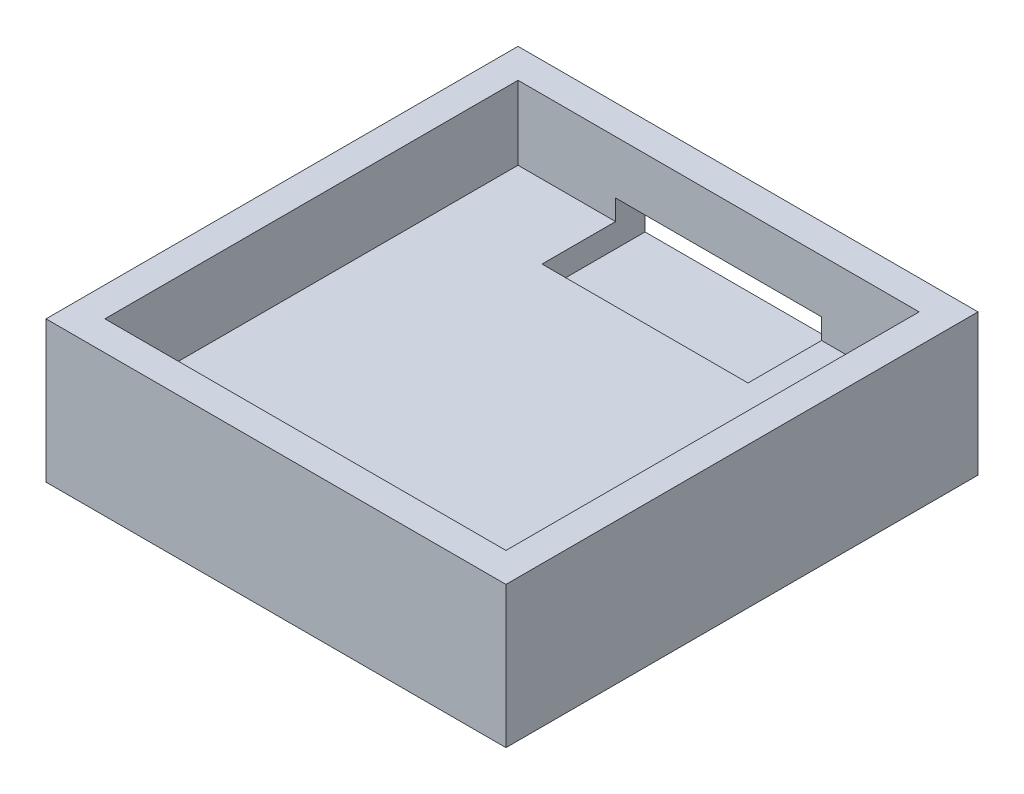
SolidWorks part; units mm, degrees
ref_plane "Front Plane" through (0, 0, 0) normal (0, 0, 1) x (1, 0, 0)
ref_plane "Top Plane" through (0, 0, 0) normal (0, 1, 0) x (1, 0, 0)
ref_plane "Right Plane" through (0, 0, 0) normal (1, 0, 0) x (0, 0, -1)
sketch "Sketch1" plane through (0, 0, 0) normal (0, 1, 0) x (1, 0, 0)
  line L0 (-10.8283, 7.7152) -> (16.4317, 7.7152)
  line L1 (-9.8283, 6.7152) -> (15.4317, 6.7152)
  line L2 (-9.8283, 6.7152) -> (-9.8283, -19.3648)
  line L3 (-9.8283, -19.3648) -> (15.4317, -19.3648)
  line L4 (15.4317, 6.7152) -> (15.4317, -19.3648)
  line L5 (16.4317, 7.7152) -> (16.4317, -20.3648)
  line L6 (-10.8283, -20.3648) -> (16.4317, -20.3648)
  line L7 (-10.8283, 7.7152) -> (-10.8283, -20.3648)
  line L8 (-12.8283, 9.7152) -> (18.4317, 9.7152)
  line L9 (18.4317, 9.7152) -> (18.4317, -22.3648)
  line L10 (-12.8283, -22.3648) -> (18.4317, -22.3648)
  line L11 (-12.8283, 9.7152) -> (-12.8283, -22.3648)
  dimension "D1" = 25.26
  dimension "D2" = 26.08
  dimension "D3" = 1
  dimension "D4" = 2
extrude "Boss-Extrude2" add sketch "Sketch1" along normal blind 1.61 contours L11 L10 L9 L8
sketch "Sketch4" plane through (0, 1.61, 0) normal (0, 1, 0) x (1, 0, 0)
  line L0 (-10.8283, 7.7152) -> (-10.8283, -20.3648)
  line L1 (-12.8283, 9.7152) -> (18.4317, 9.7152)
  line L2 (-12.8283, 9.7152) -> (-12.8283, -22.3648)
  line L3 (-12.8283, -22.3648) -> (18.4317, -22.3648)
  line L4 (18.4317, 9.7152) -> (18.4317, -22.3648)
  line L5 (-10.8283, -20.3648) -> (16.4317, -20.3648)
  line L6 (16.4317, 7.7152) -> (16.4317, -20.3648)
  line L7 (-10.8283, 7.7152) -> (16.4317, 7.7152)
  dimension "D1" = 2
extrude "Boss-Extrude3" add sketch "Sketch4" along normal blind 5
sketch "Sketch5" plane through (0, 1.61, 0) normal (0, 1, 0) x (1, 0, 0)
  line L2 (16.4317, 7.7152) -> (-10.8283, 7.7152) construction
  line L3 (-4.1983, 7.7152) -> (9.8017, 7.7152)
  line L4 (-4.1983, 7.7152) -> (-4.1983, 2.7152)
  line L5 (-4.1983, 2.7152) -> (9.8017, 2.7152)
  line L6 (9.8017, 7.7152) -> (9.8017, 2.7152)
  line L7 (2.8017, -20.3648) -> (2.8017, 7.7152) construction
  line L8 (-10.8283, -20.3648) -> (16.4317, -20.3648) construction
  line L9 (16.4317, 7.7152) -> (-10.8283, 7.7152) construction
  point P12 (2.8017, 2.7152)
  dimension "D1" = 5
  dimension "D2" = 14
  dimension "D3" = 0
extrude "Cut-Extrude3" cut sketch "Sketch5" against normal blind 5
sketch "Sketch8" plane through (0, 0, -9.7152) normal (0, 0, -1) x (-1, 0, 0)
  line L0 (12.8283, 0) -> (-18.4317, 0) construction
  line L1 (-9.8017, 0) -> (4.1983, 0)
  line L2 (-9.8017, 0) -> (-9.8017, 3)
  line L3 (-9.8017, 3) -> (4.1983, 3)
  line L4 (4.1983, 0) -> (4.1983, 3)
  dimension "D1" = 0
  dimension "D2" = 0
  dimension "D3" = 3
extrude "Cut-Extrude5" cut sketch "Sketch8" against normal blind 5 contours L2 L3 L4 L1
sketch "Sketch9" plane through (0, 0, 0) normal (0, -1, 0) x (1, 0, 0)
  line L1 (-12.8283, 22.3648) -> (18.4317, 22.3648)
  line L2 (-12.8283, 22.3648) -> (-12.8283, -9.7152)
  line L3 (-12.8283, -9.7152) -> (18.4317, -9.7152)
  line L4 (18.4317, 22.3648) -> (18.4317, -9.7152)
extrude "Boss-Extrude4" add sketch "Sketch9" along normal blind 3
sketch "Sketch10" plane through (0, -3, 0) normal (0, -1, 0) x (1, 0, 0)
  line L0 (2.8017, 22.3648) -> (2.8017, -9.7152) construction
  line L1 (18.4317, 22.3648) -> (-12.8283, 22.3648) construction
  line L2 (-12.8283, -9.7152) -> (18.4317, -9.7152) construction
  line L3 (-12.8283, 6.3248) -> (18.4317, 6.3248) construction
  line L4 (-12.8283, 22.3648) -> (-12.8283, -9.7152) construction
  line L5 (18.4317, -9.7152) -> (18.4317, 22.3648) construction
  circle A0 centre (2.8017, 15.6448) radius 2.5
  circle A1 centre (11.1017, 6.3248) radius 2.5
  circle A2 centre (-5.4983, 6.3248) radius 2.5
  circle A3 centre (2.8017, -2.9952) radius 2.5
  point P20 (2.8017, 6.3248)
  dimension "D1" = 5
  dimension "D2" = 5
  dimension "D3" = 5
  dimension "D4" = 5
  dimension "D5" = 8.3
  dimension "D6" = 8.3
  dimension "D7" = 18.64
  dimension "D8" = 9.32
extrude "Cut-Extrude6" cut sketch "Sketch10" against normal blind 2 contours A3
